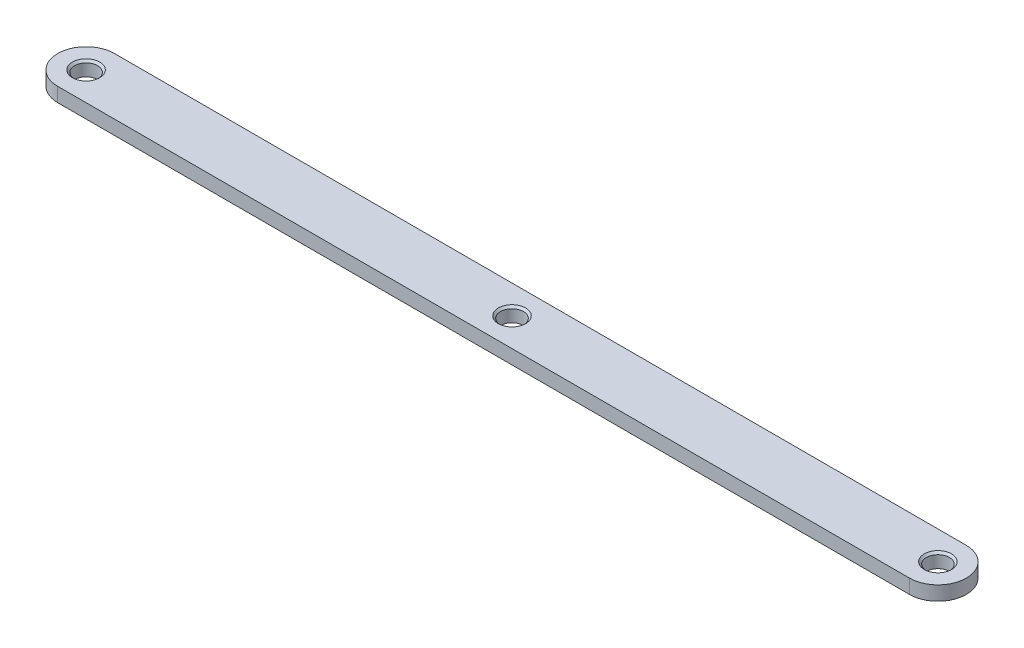
SolidWorks part; units mm, degrees
ref_plane "Front Plane" through (0, 0, 0) normal (0, 0, 1) x (1, 0, 0)
ref_plane "Top Plane" through (0, 0, 0) normal (0, 1, 0) x (1, 0, 0)
ref_plane "Right Plane" through (0, 0, 0) normal (1, 0, 0) x (0, 0, -1)
sketch "Sketch1" plane through (0, 0, 0) normal (0, 1, 0) x (1, 0, 0)
  line L0 (-95.25, 0) -> (95.25, 0) construction
  line L1 (-95.25, 6.35) -> (95.25, 6.35)
  line L2 (-95.25, -6.35) -> (95.25, -6.35)
  arc A0 (-95.25, 6.35) -> (-95.25, -6.35) centre (-95.25, 0) ccw
  arc A1 (95.25, -6.35) -> (95.25, 6.35) centre (95.25, 0) ccw
  circle A2 centre (95.25, 0) radius 2.5797
  circle A3 centre (-95.25, 0) radius 2.5797
  circle A4 centre (0, 0) radius 2.5797
  point P3 (0, 0)
  dimension "D2" = 6.35
  dimension "D3" = 5.1594
  dimension "D1" = 190.5
extrude "Boss-Extrude1" add sketch "Sketch1" along normal blind 3.175
hole_wizard "#10-32 Tapped Hole1" positions "Sketch2" profile "Sketch3" tap size "#10-32" standard "ANSI Inch" end condition through all
sketch "Sketch2" plane through (0, 3.175, 0) normal (0, 1, 0) x (1, 0, 0)
  point P0 (-95.25, 0)
  point P3 (0, 0)
  point P6 (95.25, 0)
sketch "Sketch3" plane through (-95.25, 3.175, 0) normal (1, 0, 0) x (0, 0, 1)
  line L0 (0, 0) -> (0, 3.175)
  line L1 (0, 3.175) -> (2.0193, 3.175)
  line L2 (2.0193, 3.175) -> (2.0193, 1.0287)
  line L3 (2.0193, 1.0287) -> (3.048, 0)
  line L5 (3.048, 0) -> (0, 0)
  line L6 (-2.0193, 1.0287) -> (-3.048, 0) construction
  line L11 (0, -6.35) -> (0, 107.95) construction
  dimension "Thru Tap Drill Dia." = 4.0386
  dimension "Thru Tap Drill Depth" = 3.175
  dimension "Near C'Sink Dia." = 6.096
  dimension "Near C'Sink Angle" = 90
